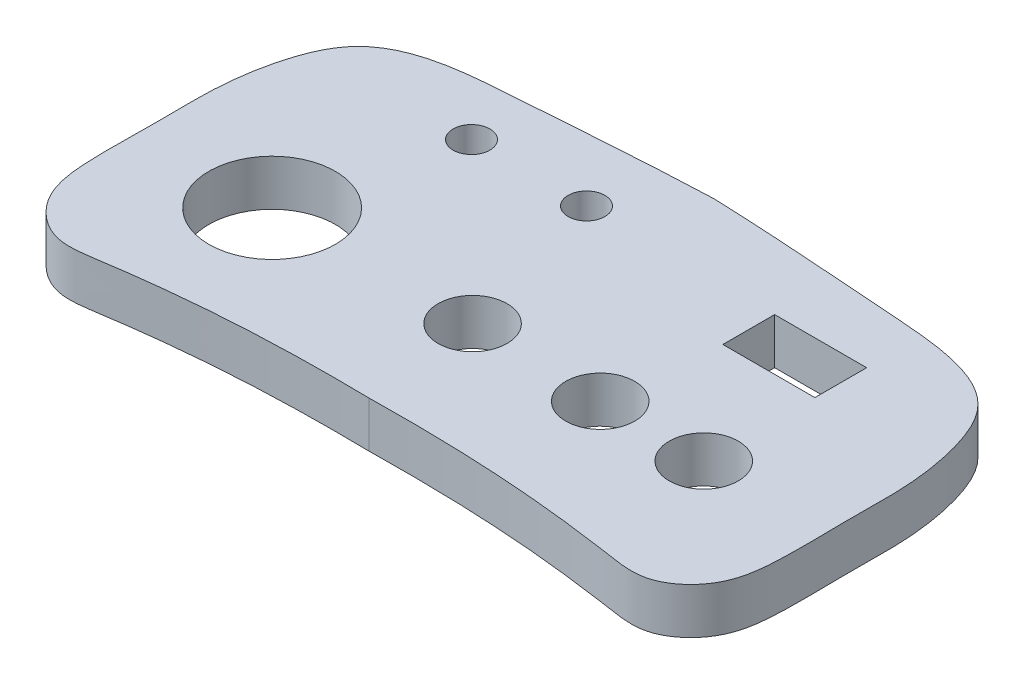
SolidWorks part; units mm, degrees
ref_plane "Ön Düzlem" through (0, 0, 0) normal (0, 0, 1) x (1, 0, 0)
ref_plane "Üst Düzlem" through (0, 0, 0) normal (0, 1, 0) x (1, 0, 0)
ref_plane "Sağ Düzlem" through (0, 0, 0) normal (1, 0, 0) x (0, 0, -1)
sketch "Çizim1" plane through (0, 0, 0) normal (0, 1, 0) x (1, 0, 0)
  line L0 (0, 17.9288) -> (0, -12.0712) construction
  line L1 (0, 0) -> (-30, 0) construction
  line L2 (-108.3091, -42.1463) -> (-63.9653, -42.1463) construction
  spline S0 degree 3 poles (0, 17.9288) (-5.8202, 17.7095) (-13.9034, 17.0426) (-26.8757, 16.196) (-29.5503, 8.9293) (-30.0905, 4.3361) (-29.9407, -0.8874) (-30.1549, -5.7017) (-29.6372, -10.9288) (-26.0312, -14.0818) (-15.7201, -12.3493) (-7.8072, -11.9389) (0, -12.0712) knots 0 0 0 0 0.19846 0.336013 0.394477 0.45973 0.505377 0.582751 0.635933 0.690009 0.731881 1 1 1 1
  spline S1 degree 3 poles (0, 17.9288) (5.8202, 17.7095) (13.9034, 17.0426) (26.8757, 16.196) (29.5503, 8.9293) (30.0905, 4.3361) (29.9407, -0.8874) (30.1549, -5.7017) (29.6372, -10.9288) (26.0312, -14.0818) (15.7201, -12.3493) (7.8072, -11.9389) (0, -12.0712) knots 0 0 0 0 0.19846 0.336013 0.394477 0.45973 0.505377 0.582751 0.635933 0.690009 0.731881 1 1 1 1
  dimension "D1" = 30
  dimension "D2" = 30
extrude "Yükseklik-Ekstrüzyon1" add sketch "Çizim1" along normal blind 4
sketch "Çizim2" plane through (0, 4, 0) normal (0, 1, 0) x (1, 0, 0)
  line L1 (11.3495, 11.842) -> (19.3495, 11.842)
  line L2 (11.3495, 11.842) -> (11.3495, 7.342)
  line L3 (11.3495, 7.342) -> (19.3495, 7.342)
  line L4 (19.3495, 11.842) -> (19.3495, 7.342)
  circle A0 centre (-18.5277, -1.9625) radius 5.5
  circle A1 centre (-1.1023, -1.9625) radius 3
  circle A2 centre (10.2935, -2.262) radius 3
  circle A3 centre (19.2935, -2.262) radius 3
  circle A4 centre (-15.002, 11.842) radius 1.6
  circle A5 centre (-5.002, 11.842) radius 1.6
  spline S0 degree 3 poles (0, 17.9288) (-5.8202, 17.7095) (-13.9034, 17.0426) (-26.8757, 16.196) (-29.5503, 8.9293) (-30.0905, 4.3361) (-29.9407, -0.8874) (-30.1549, -5.7017) (-29.6372, -10.9288) (-26.0312, -14.0818) (-15.7201, -12.3493) (-7.8072, -11.9389) (0, -12.0712) knots 0 0 0 0 0.19846 0.336013 0.394477 0.45973 0.505377 0.582751 0.635933 0.690009 0.731881 1 1 1 1 construction
  point P12 (-30.002, 0.4453)
  dimension "D1" = 11
  dimension "D2" = 6
  dimension "D3" = 9
  dimension "D4" = 6
  dimension "D5" = 10
  dimension "D9" = 3.2
  dimension "D10" = 3.2
  dimension "D6" = 15
  dimension "D7" = 8
  dimension "D8" = 4.5
extrude "Kes-Ekstrüzyon1" cut sketch "Çizim2" against normal blind 10
